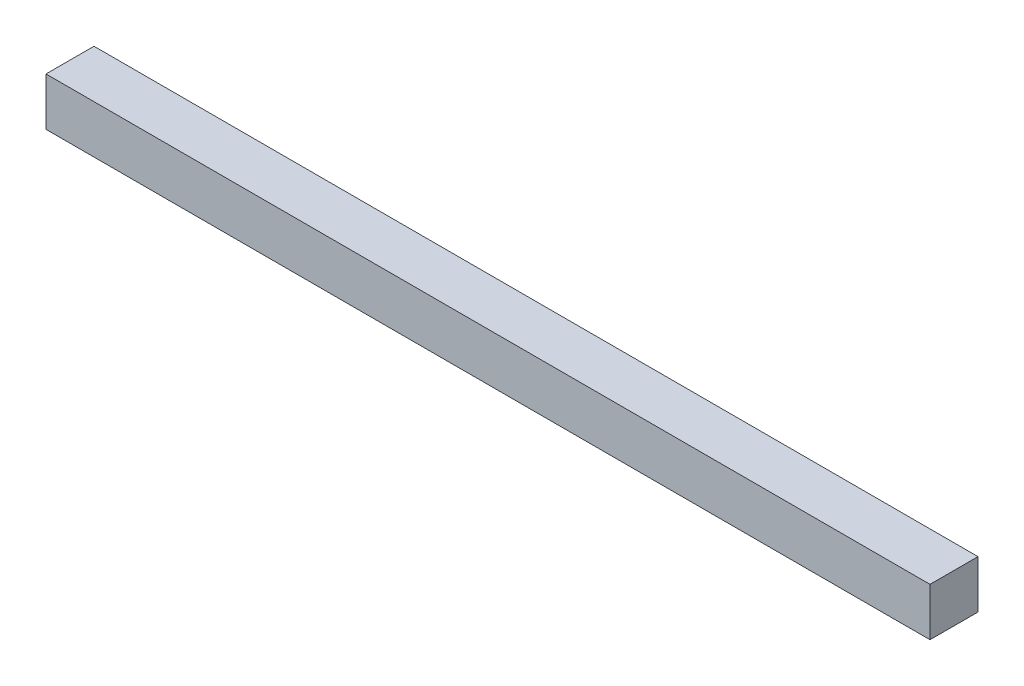
SolidWorks part; units mm, degrees
material "Cedar"
ref_plane "Front Plane" through (0, 0, 0) normal (0, 0, 1) x (1, 0, 0)
ref_plane "Top Plane" through (0, 0, 0) normal (0, 1, 0) x (1, 0, 0)
ref_plane "Right Plane" through (0, 0, 0) normal (1, 0, 0) x (0, 0, -1)
sketch "Sketch1" plane through (0, 0, 0) normal (1, 0, 0) x (0, 0, -1)
  line L1 (-19.05, -19.05) -> (19.05, -19.05)
  line L2 (-19.05, -19.05) -> (-19.05, 19.05)
  line L3 (-19.05, 19.05) -> (19.05, 19.05)
  line L4 (19.05, -19.05) -> (19.05, 19.05)
  line L5 (-19.05, -19.05) -> (19.05, 19.05) construction
  line L6 (-19.05, 19.05) -> (19.05, -19.05) construction
  point P0 (0, 0)
  dimension "D1" = 38.1
  dimension "D2" = 38.1
extrude "Boss-Extrude1" add sketch "Sketch1" along normal blind 701.675
